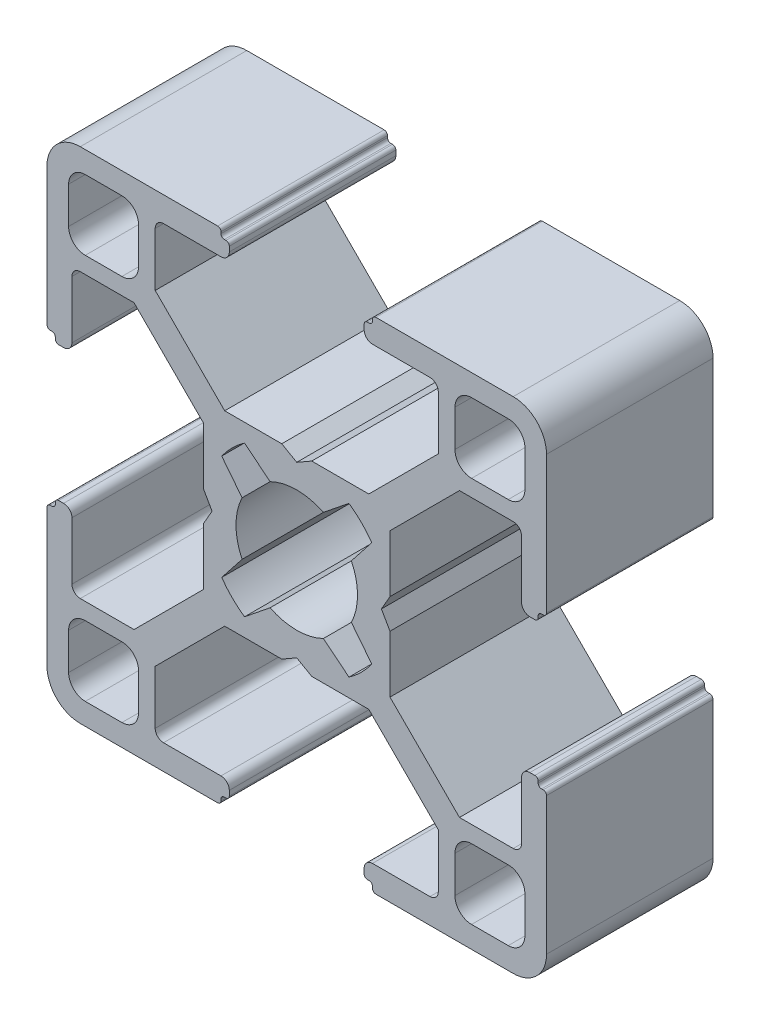
SolidWorks part; units mm, degrees
ref_plane "Спереди" through (0, 0, 0) normal (0, 0, 1) x (1, 0, 0)
ref_plane "Сверху" through (0, 0, 0) normal (0, 1, 0) x (1, 0, 0)
ref_plane "Справа" through (0, 0, 0) normal (1, 0, 0) x (0, 0, -1)
sketch "Эскиз1" plane through (0, 0, 0) normal (0, 0, 1) x (1, 0, 0)
  line L43 (-4.05, 14.3) -> (-4.05, 14)
  line L44 (-4.25, 14.5) -> (-4.35, 14.5)
  line L45 (-4.55, 14.8) -> (-4.55, 14.7)
  line L46 (-4.75, 15) -> (-13, 15)
  line L74 (-3.2806, 1.6001) -> (-4.5053, 3.1547)
  line L75 (-3.1359, 4.5184) -> (-1.6001, 3.2806)
  line L76 (-10.5, 13.7) -> (-12.7, 13.7)
  line L77 (-9.5, 12.7) -> (-9.5, 10.5)
  line L78 (-10.5, 9.5) -> (-12.7, 9.5)
  line L79 (-13.7, 12.7) -> (-13.7, 10.5)
  line L80 (-5.0849, 0) -> (5.0849, 0) construction
  line L81 (0, -5.0849) -> (0, 5.0849) construction
  line L82 (-5.6, 0.9) -> (-5.0849, 0)
  line L88 (0, 0) -> (-3.8891, 3.8891) construction
  line L89 (-8.5, 9.7728) -> (-4.3272, 5.6)
  line L99 (-0.9, 5.6) -> (0, 5.0849)
  line L100 (-8.5, 13) -> (-8.5, 9.7728)
  line L101 (-4.3272, 5.6) -> (-0.9, 5.6)
  line L102 (-8, 13.5) -> (-4.55, 13.5)
  line L106 (-13.5, 8) -> (-13.5, 4.55)
  line L107 (-5.6, 4.3272) -> (-5.6, 0.9)
  line L112 (-13, 8.5) -> (-9.7728, 8.5)
  line L113 (-9.7728, 8.5) -> (-5.6, 4.3272)
  line L114 (-15, 4.75) -> (-15, 13)
  line L115 (-14.8, 4.55) -> (-14.7, 4.55)
  line L116 (-14.5, 4.25) -> (-14.5, 4.35)
  line L117 (-14.3, 4.05) -> (-14, 4.05)
  line L118 (0.9, 5.6) -> (0, 5.0849)
  line L119 (5.6, 0.9) -> (5.0849, 0)
  line L122 (14.3, 4.05) -> (14, 4.05)
  line L123 (14.5, 4.25) -> (14.5, 4.35)
  line L124 (14.8, 4.55) -> (14.7, 4.55)
  line L125 (15, 4.75) -> (15, 13)
  line L126 (9.7728, 8.5) -> (5.6, 4.3272)
  line L127 (13, 8.5) -> (9.7728, 8.5)
  line L128 (5.6, 4.3272) -> (5.6, 0.9)
  line L129 (13.5, 8) -> (13.5, 4.55)
  line L130 (8, 13.5) -> (4.55, 13.5)
  line L131 (4.3272, 5.6) -> (0.9, 5.6)
  line L132 (8.5, 13) -> (8.5, 9.7728)
  line L133 (8.5, 9.7728) -> (4.3272, 5.6)
  line L134 (13.7, 12.7) -> (13.7, 10.5)
  line L135 (10.5, 9.5) -> (12.7, 9.5)
  line L136 (9.5, 12.7) -> (9.5, 10.5)
  line L137 (10.5, 13.7) -> (12.7, 13.7)
  line L138 (3.1359, 4.5184) -> (1.6001, 3.2806)
  line L139 (3.2806, 1.6001) -> (4.5053, 3.1547)
  line L140 (4.75, 15) -> (13, 15)
  line L141 (4.55, 14.8) -> (4.55, 14.7)
  line L142 (4.25, 14.5) -> (4.35, 14.5)
  line L143 (4.05, 14.3) -> (4.05, 14)
  line L150 (0, 0) -> (-3.8891, -3.8891) construction
  line L152 (4.05, -14.3) -> (4.05, -14)
  line L153 (4.25, -14.5) -> (4.35, -14.5)
  line L154 (4.55, -14.8) -> (4.55, -14.7)
  line L155 (4.75, -15) -> (13, -15)
  line L156 (3.2806, -1.6001) -> (4.5053, -3.1547)
  line L157 (3.1359, -4.5184) -> (1.6001, -3.2806)
  line L158 (10.5, -13.7) -> (12.7, -13.7)
  line L159 (9.5, -12.7) -> (9.5, -10.5)
  line L160 (10.5, -9.5) -> (12.7, -9.5)
  line L161 (13.7, -12.7) -> (13.7, -10.5)
  line L162 (8.5, -9.7728) -> (4.3272, -5.6)
  line L163 (8.5, -13) -> (8.5, -9.7728)
  line L164 (4.3272, -5.6) -> (0.9, -5.6)
  line L165 (8, -13.5) -> (4.55, -13.5)
  line L166 (13.5, -8) -> (13.5, -4.55)
  line L167 (5.6, -4.3272) -> (5.6, -0.9)
  line L168 (13, -8.5) -> (9.7728, -8.5)
  line L169 (9.7728, -8.5) -> (5.6, -4.3272)
  line L170 (15, -4.75) -> (15, -13)
  line L171 (14.8, -4.55) -> (14.7, -4.55)
  line L172 (14.5, -4.25) -> (14.5, -4.35)
  line L173 (14.3, -4.05) -> (14, -4.05)
  line L174 (5.6, -0.9) -> (5.0849, 0)
  line L175 (0.9, -5.6) -> (0, -5.0849)
  line L176 (-14.3, -4.05) -> (-14, -4.05)
  line L177 (-14.5, -4.25) -> (-14.5, -4.35)
  line L178 (-14.8, -4.55) -> (-14.7, -4.55)
  line L179 (-15, -4.75) -> (-15, -13)
  line L180 (-9.7728, -8.5) -> (-5.6, -4.3272)
  line L181 (-13, -8.5) -> (-9.7728, -8.5)
  line L182 (-5.6, -4.3272) -> (-5.6, -0.9)
  line L183 (-13.5, -8) -> (-13.5, -4.55)
  line L184 (-8, -13.5) -> (-4.55, -13.5)
  line L185 (-4.3272, -5.6) -> (-0.9, -5.6)
  line L186 (-8.5, -13) -> (-8.5, -9.7728)
  line L187 (-0.9, -5.6) -> (0, -5.0849)
  line L188 (-8.5, -9.7728) -> (-4.3272, -5.6)
  line L189 (-5.6, -0.9) -> (-5.0849, 0)
  line L190 (-13.7, -12.7) -> (-13.7, -10.5)
  line L191 (-10.5, -9.5) -> (-12.7, -9.5)
  line L192 (-9.5, -12.7) -> (-9.5, -10.5)
  line L193 (-10.5, -13.7) -> (-12.7, -13.7)
  line L194 (-3.1359, -4.5184) -> (-1.6001, -3.2806)
  line L195 (-3.2806, -1.6001) -> (-4.5053, -3.1547)
  line L196 (-4.75, -15) -> (-13, -15)
  line L197 (-4.55, -14.8) -> (-4.55, -14.7)
  line L198 (-4.25, -14.5) -> (-4.35, -14.5)
  line L199 (-4.05, -14.3) -> (-4.05, -14)
  arc A4 (1.6001, 3.2806) -> (-1.6001, 3.2806) centre (0, 0) ccw
  arc A25 (-3.2806, 1.6001) -> (-3.2806, -1.6001) centre (0, 0) ccw
  arc A26 (-4.05, 14.3) -> (-4.25, 14.5) centre (-4.25, 14.3) ccw
  arc A27 (-4.35, 14.5) -> (-4.55, 14.7) centre (-4.35, 14.7) cw
  arc A28 (-4.55, 14.8) -> (-4.75, 15) centre (-4.75, 14.8) ccw
  arc A29 (-13, 15) -> (-15, 13) centre (-13, 13) ccw
  arc A33 (-4.5053, 3.1547) -> (-3.1359, 4.5184) centre (0, 0) cw
  arc A48 (-10.5, 13.7) -> (-9.5, 12.7) centre (-10.5, 12.7) cw
  arc A49 (-9.5, 10.5) -> (-10.5, 9.5) centre (-10.5, 10.5) cw
  arc A50 (-12.7, 9.5) -> (-13.7, 10.5) centre (-12.7, 10.5) cw
  arc A51 (-13.7, 12.7) -> (-12.7, 13.7) centre (-12.7, 12.7) cw
  arc A68 (-8.5, 13) -> (-8, 13.5) centre (-8, 13) cw
  arc A69 (-4.05, 14) -> (-4.55, 13.5) centre (-4.55, 14) cw
  arc A70 (-14, 4.05) -> (-13.5, 4.55) centre (-14, 4.55) ccw
  arc A71 (-13, 8.5) -> (-13.5, 8) centre (-13, 8) ccw
  arc A72 (-14.8, 4.55) -> (-15, 4.75) centre (-14.8, 4.75) cw
  arc A73 (-14.5, 4.35) -> (-14.7, 4.55) centre (-14.7, 4.35) ccw
  arc A74 (-14.3, 4.05) -> (-14.5, 4.25) centre (-14.3, 4.25) cw
  arc A75 (3.2806, 1.6001) -> (3.2806, -1.6001) centre (0, 0) cw
  arc A76 (14.3, 4.05) -> (14.5, 4.25) centre (14.3, 4.25) ccw
  arc A77 (14.5, 4.35) -> (14.7, 4.55) centre (14.7, 4.35) cw
  arc A78 (14.8, 4.55) -> (15, 4.75) centre (14.8, 4.75) ccw
  arc A79 (13, 8.5) -> (13.5, 8) centre (13, 8) cw
  arc A80 (14, 4.05) -> (13.5, 4.55) centre (14, 4.55) cw
  arc A81 (4.05, 14) -> (4.55, 13.5) centre (4.55, 14) ccw
  arc A82 (8.5, 13) -> (8, 13.5) centre (8, 13) ccw
  arc A83 (13.7, 12.7) -> (12.7, 13.7) centre (12.7, 12.7) ccw
  arc A84 (12.7, 9.5) -> (13.7, 10.5) centre (12.7, 10.5) ccw
  arc A85 (9.5, 10.5) -> (10.5, 9.5) centre (10.5, 10.5) ccw
  arc A86 (10.5, 13.7) -> (9.5, 12.7) centre (10.5, 12.7) ccw
  arc A87 (4.5053, 3.1547) -> (3.1359, 4.5184) centre (0, 0) ccw
  arc A88 (13, 15) -> (15, 13) centre (13, 13) cw
  arc A89 (4.55, 14.8) -> (4.75, 15) centre (4.75, 14.8) cw
  arc A90 (4.35, 14.5) -> (4.55, 14.7) centre (4.35, 14.7) ccw
  arc A91 (4.05, 14.3) -> (4.25, 14.5) centre (4.25, 14.3) cw
  arc A92 (4.05, -14.3) -> (4.25, -14.5) centre (4.25, -14.3) ccw
  arc A93 (4.35, -14.5) -> (4.55, -14.7) centre (4.35, -14.7) cw
  arc A94 (4.55, -14.8) -> (4.75, -15) centre (4.75, -14.8) ccw
  arc A95 (13, -15) -> (15, -13) centre (13, -13) ccw
  arc A96 (4.5053, -3.1547) -> (3.1359, -4.5184) centre (0, 0) cw
  arc A97 (10.5, -13.7) -> (9.5, -12.7) centre (10.5, -12.7) cw
  arc A98 (9.5, -10.5) -> (10.5, -9.5) centre (10.5, -10.5) cw
  arc A99 (12.7, -9.5) -> (13.7, -10.5) centre (12.7, -10.5) cw
  arc A100 (13.7, -12.7) -> (12.7, -13.7) centre (12.7, -12.7) cw
  arc A101 (8.5, -13) -> (8, -13.5) centre (8, -13) cw
  arc A102 (4.05, -14) -> (4.55, -13.5) centre (4.55, -14) cw
  arc A103 (14, -4.05) -> (13.5, -4.55) centre (14, -4.55) ccw
  arc A104 (13, -8.5) -> (13.5, -8) centre (13, -8) ccw
  arc A105 (14.8, -4.55) -> (15, -4.75) centre (14.8, -4.75) cw
  arc A106 (14.5, -4.35) -> (14.7, -4.55) centre (14.7, -4.35) ccw
  arc A107 (14.3, -4.05) -> (14.5, -4.25) centre (14.3, -4.25) cw
  arc A108 (-14.3, -4.05) -> (-14.5, -4.25) centre (-14.3, -4.25) ccw
  arc A109 (-14.5, -4.35) -> (-14.7, -4.55) centre (-14.7, -4.35) cw
  arc A110 (-14.8, -4.55) -> (-15, -4.75) centre (-14.8, -4.75) ccw
  arc A111 (-13, -8.5) -> (-13.5, -8) centre (-13, -8) cw
  arc A112 (-14, -4.05) -> (-13.5, -4.55) centre (-14, -4.55) cw
  arc A113 (-4.05, -14) -> (-4.55, -13.5) centre (-4.55, -14) ccw
  arc A114 (-8.5, -13) -> (-8, -13.5) centre (-8, -13) ccw
  arc A115 (-13.7, -12.7) -> (-12.7, -13.7) centre (-12.7, -12.7) ccw
  arc A116 (-12.7, -9.5) -> (-13.7, -10.5) centre (-12.7, -10.5) ccw
  arc A117 (-9.5, -10.5) -> (-10.5, -9.5) centre (-10.5, -10.5) ccw
  arc A118 (-10.5, -13.7) -> (-9.5, -12.7) centre (-10.5, -12.7) ccw
  arc A119 (-4.5053, -3.1547) -> (-3.1359, -4.5184) centre (0, 0) ccw
  arc A120 (-13, -15) -> (-15, -13) centre (-13, -13) cw
  arc A121 (-4.55, -14.8) -> (-4.75, -15) centre (-4.75, -14.8) cw
  arc A122 (-4.35, -14.5) -> (-4.55, -14.7) centre (-4.35, -14.7) ccw
  arc A123 (-4.05, -14.3) -> (-4.25, -14.5) centre (-4.25, -14.3) cw
  arc A124 (1.6001, -3.2806) -> (-1.6001, -3.2806) centre (0, 0) cw
  point P82 (0, 15)
  point P107 (15, 15)
  point P202 (0, 0)
  point P203 (15, 0)
  point P215 (-15, 0)
  point P217 (-15, 15)
  point P265 (-15, -15)
  point P266 (15, -15)
  point P267 (0, -15)
  dimension "D6" = 0.5
  dimension "D2" = 0.5
  dimension "D3" = 1.5
  dimension "D4" = 1
  dimension "D5" = 0.9
  dimension "D8" = 15
extrude "Бобышка-Вытянуть1" add sketch "Эскиз1" along normal blind 10
